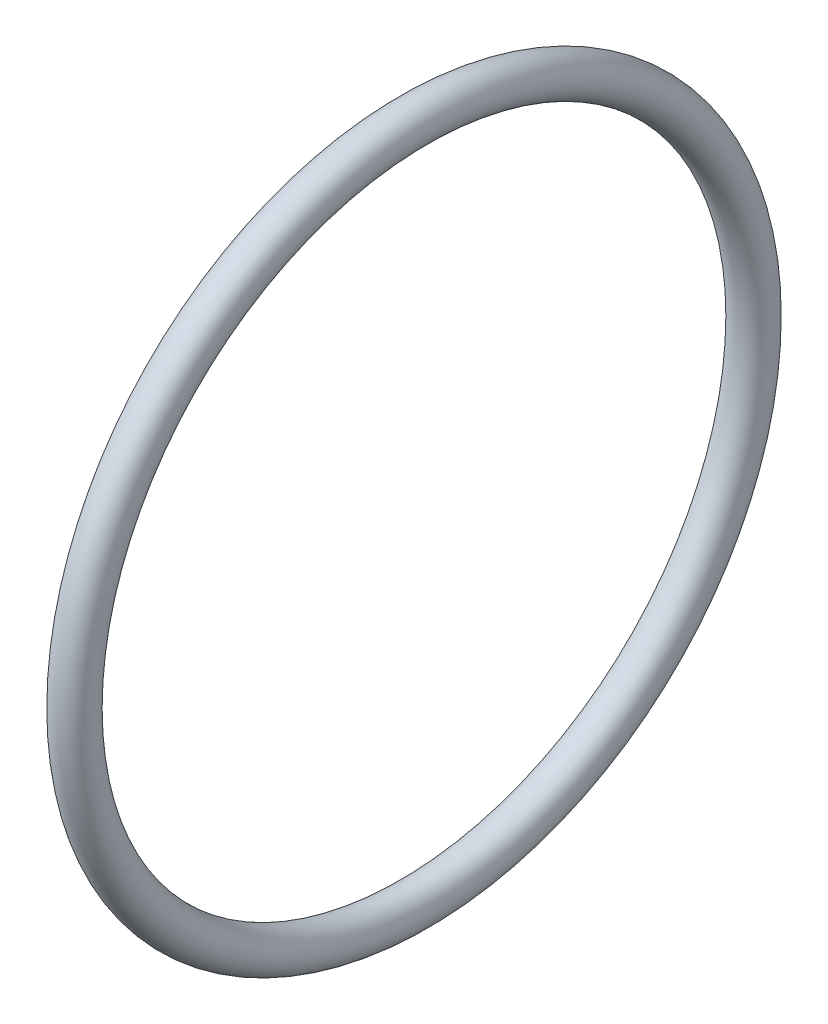
SolidWorks part; units mm, degrees
ref_plane "Спереди" through (0, 0, 0) normal (0, 0, 1) x (1, 0, 0)
ref_plane "Сверху" through (0, 0, 0) normal (0, 1, 0) x (1, 0, 0)
ref_plane "Справа" through (0, 0, 0) normal (1, 0, 0) x (0, 0, -1)
sketch "Эскиз4" plane through (0, 0, 0) normal (0, 1, 0) x (1, 0, 0)
  circle A0 centre (0, 24.6113) radius 1.0792
sketch "Эскиз5" plane through (0, 0, 0) normal (0, 1, 0) x (1, 0, 0)
  line L1 (-35.8611, 0) -> (37.7877, 0) construction
  circle A0 centre (-2.1142, 13) radius 0.75
  dimension "D2" = 1.5
  dimension "D1" = 13
revolve "Повернуть1" add sketch "Эскиз5" angle 360 about L1
sketch "Эскиз6" plane through (0, 0, 0) normal (1, 0, 0) x (0, 0, -1)
  circle A0 centre (0, 0) radius 12.9867
